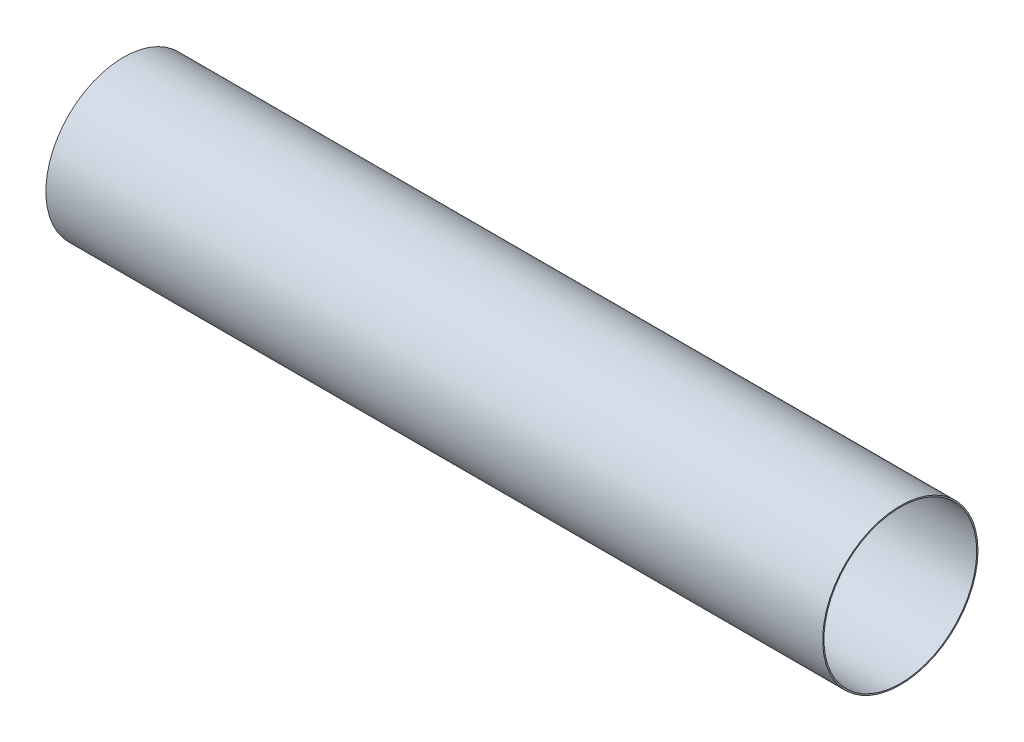
SolidWorks part; units mm, degrees
material "S-Glass Fiber"
ref_plane "Front Plane" through (0, 0, 0) normal (0, 0, 1) x (1, 0, 0)
ref_plane "Top Plane" through (0, 0, 0) normal (0, 1, 0) x (1, 0, 0)
ref_plane "Right Plane" through (0, 0, 0) normal (1, 0, 0) x (0, 0, -1)
sketch "Sketch2" plane through (0, 0, 0) normal (1, 0, 0) x (0, 0, -1)
  circle A0 centre (0, 0) radius 76.2
  circle A1 centre (0, 0) radius 74.93
  dimension "D1" = 152.4
  dimension "D2" = 149.86
extrude "Boss-Extrude1" add sketch "Sketch2" against normal mid plane 762
